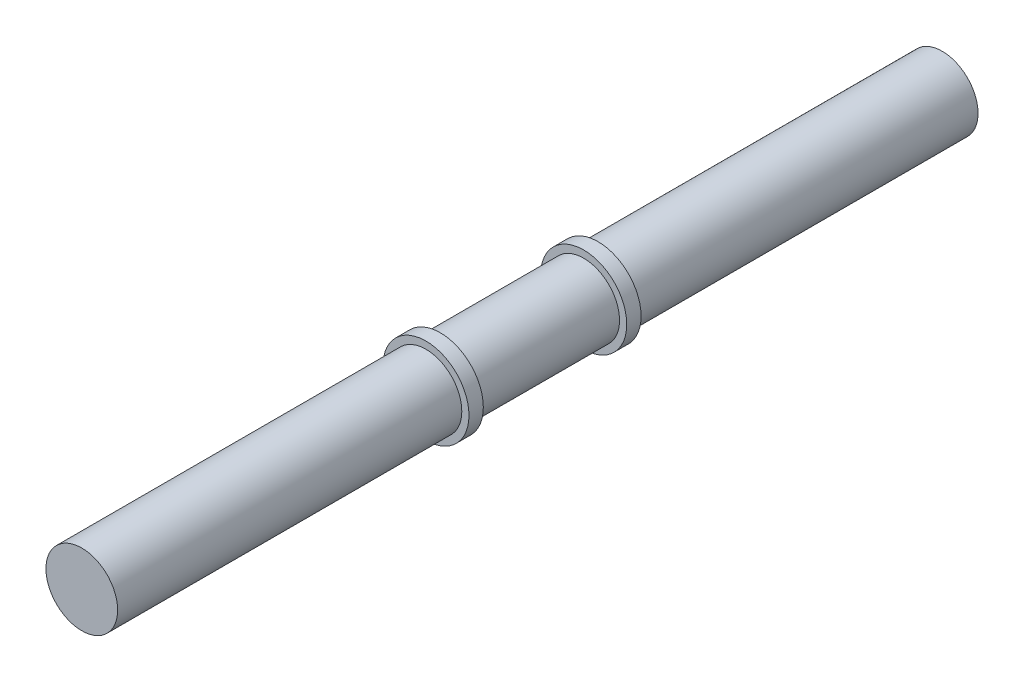
SolidWorks part; units mm, degrees
ref_plane "Front Plane" through (0, 0, 0) normal (0, 0, 1) x (1, 0, 0)
ref_plane "Top Plane" through (0, 0, 0) normal (0, 1, 0) x (1, 0, 0)
ref_plane "Right Plane" through (0, 0, 0) normal (1, 0, 0) x (0, 0, -1)
sketch "Sketch1" plane through (0, 0, 0) normal (0, 0, 1) x (1, 0, 0)
  circle A0 centre (0, 0) radius 5
  dimension "D1" = 10
extrude "Boss-Extrude1" add sketch "Sketch1" along normal blind 191.48
ref_plane "Plane1" through (0, 0, 95.74) normal (0, 0, 1) x (1, 0, 0)
ref_plane "Plane2" through (0, 0, 105.74) normal (0, 0, 1) x (1, 0, 0)
sketch "Sketch2" plane through (0, 0, 105.74) normal (0, 0, 1) x (1, 0, 0)
  circle A0 centre (0, 0) radius 6
  dimension "D1" = 12
extrude "Boss-Extrude2" add sketch "Sketch2" along normal blind 2
mirror "Mirror1" about plane through (0, 0, 95.74) normal (0, 0, 1) of "Boss-Extrude2"
sketch "Sketch3" plane through (0, 0, 191.48) normal (0, 0, 1) x (1, 0, 0)
  circle A0 centre (0, 0) radius 5
extrude "Cut-Extrude1" cut sketch "Sketch3" against normal blind 35.74
sketch "Sketch4" plane through (0, 0, 0) normal (0, 0, -1) x (-1, 0, 0)
  circle A0 centre (0, 0) radius 5
extrude "Cut-Extrude2" cut sketch "Sketch4" against normal blind 35.74
